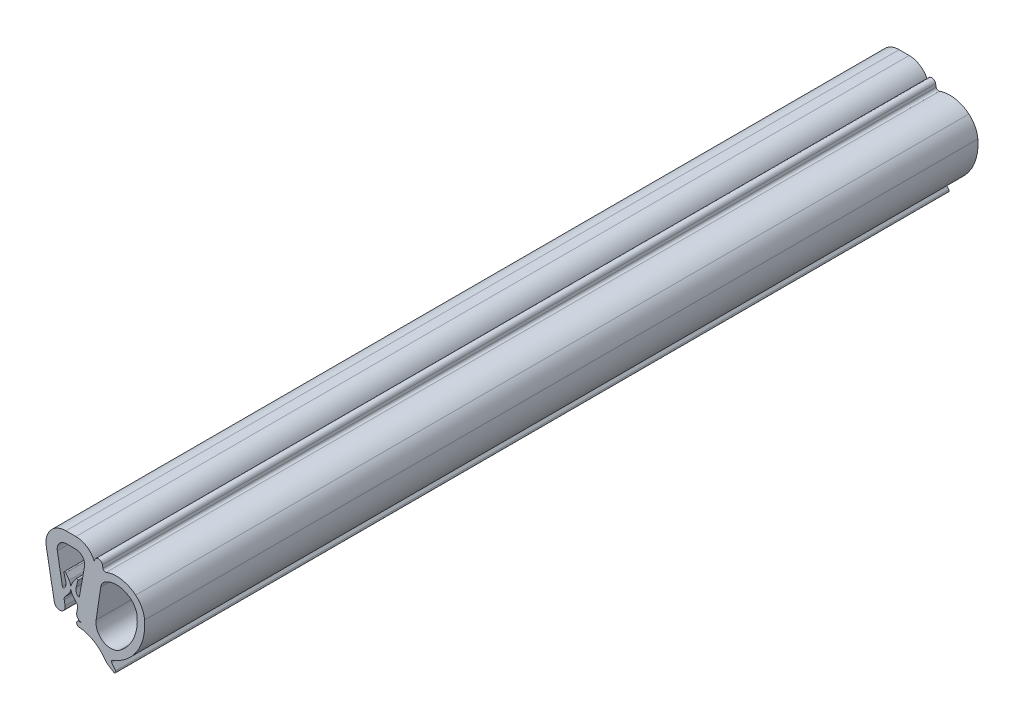
SolidWorks part; units mm, degrees
ref_plane "Ebene vorne" through (0, 0, 0) normal (0, 0, 1) x (1, 0, 0)
ref_plane "Ebene oben" through (0, 0, 0) normal (0, 1, 0) x (1, 0, 0)
ref_plane "Ebene rechts" through (0, 0, 0) normal (1, 0, 0) x (0, 0, -1)
sketch "Skizze2" plane through (0, 0, 0) normal (0, 0, 1) x (1, 0, 0)
  line L0 (9.8324, -17.6) -> (7.353, -17.6) construction
  line L1 (14.8, 2.8992) -> (14.8, -11.7833) construction
  line L2 (5.9667, -4.1113) -> (5.0461, -10.2699)
  line L11 (2.2495, -12.203) -> (1.6495, -12.203)
  line L12 (7.5515, -16.9065) -> (8.5356, -17.551)
  line L13 (8.94, -17.12) -> (8.16, -16.08)
  line L29 (1, 2.2) -> (-1, 2.2)
  line L30 (-4.935, -2.5184) -> (-3.3321, -11.2976)
  line L31 (-1.1668, -10.9084) -> (-1.3382, -9.9393)
  line L32 (-1.1541, -9.275) -> (-0.4935, -8.5154)
  line L33 (-0.3615, -6.0531) -> (-1.0359, -5.0856)
  line L34 (-1.3935, -5.2504) -> (-1.0484, -6.5752)
  line L35 (-1.7105, -7.8348) -> (-2.7225, -2.1135)
  line L36 (-0.95, 0) -> (0.95, 0)
  line L37 (2.7225, -2.1135) -> (1.7105, -7.8348)
  line L38 (1.0484, -6.5752) -> (1.3935, -5.2504)
  line L39 (1.0359, -5.0856) -> (0.3615, -6.0531)
  line L40 (0.4935, -8.5154) -> (1.1541, -9.275)
  line L41 (1.3382, -9.9393) -> (1.1663, -10.9114)
  line L42 (6.4078, -0.5882) -> (6.3129, -0.0588)
  arc A10 (9.7658, -13.1482) -> (13.2699, -5.5352) centre (4.8, -6.2496) ccw
  arc A11 (5.0461, -10.2699) -> (9.7658, -13.1482) centre (8.0131, -10.7134) ccw
  arc A32 (1.1663, -10.9114) -> (2.2495, -12.203) centre (2.2495, -11.103) ccw
  arc A33 (4.7712, -0.4667) -> (1, 2.2) centre (1, -1.8) ccw
  arc A34 (-1, 2.2) -> (-4.935, -2.5184) centre (-1, -1.8) ccw
  arc A35 (-3.3321, -11.2976) -> (-1.1668, -10.9084) centre (-2.25, -11.1) ccw
  arc A36 (-1.1541, -9.275) -> (-1.3382, -9.9393) centre (-0.5505, -9.8) ccw
  arc A37 (-0.4935, -8.5154) -> (-0.3615, -6.0531) centre (-2.0063, -7.1997) ccw
  arc A38 (-1.0359, -5.0856) -> (-1.3935, -5.2504) centre (-1.2, -5.2) ccw
  arc A39 (-1.3618, -7.9303) -> (-1.0484, -6.5752) centre (-2.5, -6.9533) ccw
  arc A40 (-1.7105, -7.8348) -> (-1.3618, -7.9303) centre (-1.5135, -7.8) ccw
  arc A41 (-0.95, 0) -> (-2.7225, -2.1135) centre (-0.95, -1.8) ccw
  arc A42 (2.7225, -2.1135) -> (0.95, 0) centre (0.95, -1.8) ccw
  arc A43 (1.3618, -7.9303) -> (1.7105, -7.8348) centre (1.5135, -7.8) ccw
  arc A44 (1.0484, -6.5752) -> (1.3618, -7.9303) centre (2.5, -6.9533) ccw
  arc A45 (1.3935, -5.2504) -> (1.0359, -5.0856) centre (1.2, -5.2) ccw
  arc A46 (0.3615, -6.0531) -> (0.4935, -8.5154) centre (2.0063, -7.1997) ccw
  arc A47 (1.3382, -9.9393) -> (1.1541, -9.275) centre (0.5505, -9.8) ccw
  arc A56 (6.3129, -0.0588) -> (4.7712, -0.4667) centre (5.5255, -0.2) ccw
  arc A59 (1.6495, -12.203) -> (1.6085, -13.2013) centre (1.6495, -12.703) ccw
  arc A60 (6.7472, -16.1311) -> (1.6085, -13.2013) centre (1.0354, -20.1778) ccw
  arc A61 (6.7472, -16.1311) -> (7.5515, -16.9065) centre (9.1951, -14.3968) ccw
  arc A62 (8.5356, -17.551) -> (8.94, -17.12) centre (8.7, -17.3) ccw
  arc A63 (8.2951, -15.6189) -> (8.16, -16.08) centre (8.4, -15.9) ccw
  arc A64 (8.2951, -15.6189) -> (14.7646, -5.4092) centre (4.8, -6.2496) ccw
  arc A65 (14.7646, -5.4092) -> (12.9689, -1.9764) centre (9.7823, -5.8294) ccw
  arc A66 (12.9689, -1.9764) -> (7.0727, -0.9692) centre (9.145, -6.6) ccw
  arc A67 (6.4078, -0.5882) -> (7.0727, -0.9692) centre (6.9, -0.5) ccw
  arc A68 (6.9845, -2.6526) -> (5.9667, -4.1113) centre (7.9447, -4.407) ccw
  arc A69 (12.0129, -3.1323) -> (6.9845, -2.6526) centre (9.145, -6.6) ccw
  arc A70 (13.2699, -5.5352) -> (12.0129, -3.1323) centre (9.7823, -5.8294) ccw
extrude "Aufsatz-Linear austragen1" add sketch "Skizze2" along normal blind 167
